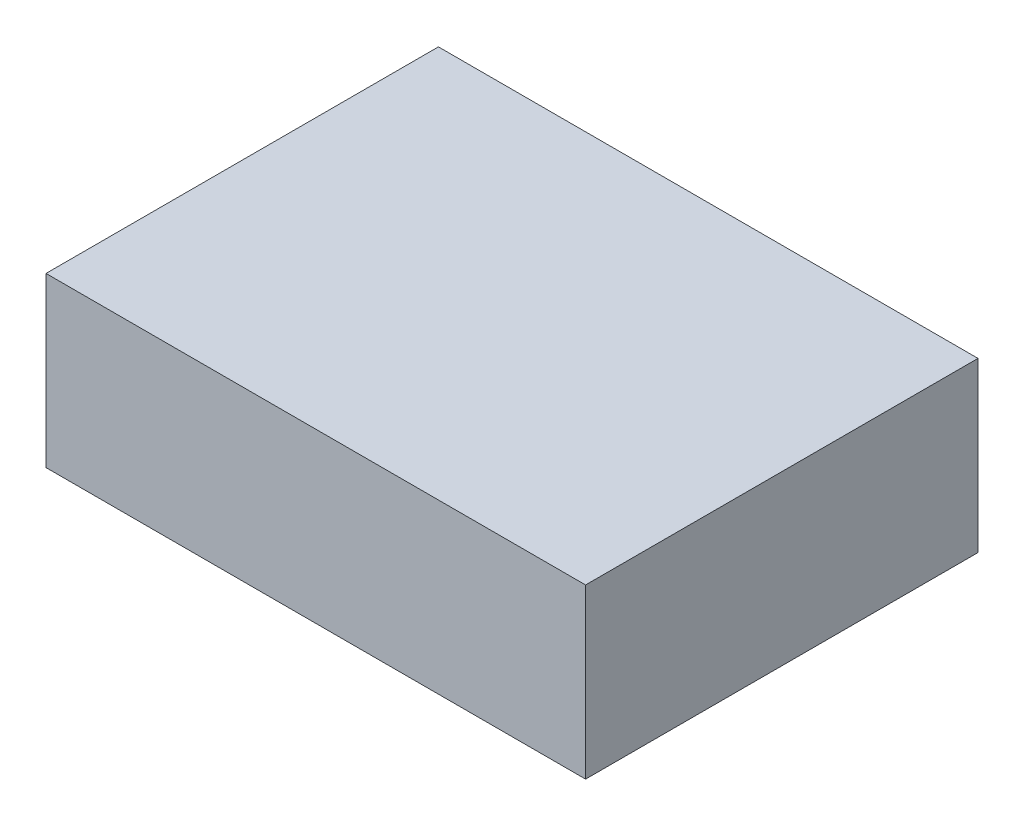
SolidWorks part; units mm, degrees
material "Pine"
ref_plane "Front Plane" through (0, 0, 0) normal (0, 0, 1) x (1, 0, 0)
ref_plane "Top Plane" through (0, 0, 0) normal (0, 1, 0) x (1, 0, 0)
ref_plane "Right Plane" through (0, 0, 0) normal (1, 0, 0) x (0, 0, -1)
sketch "Sketch1" plane through (0, 0, 0) normal (0, 1, 0) x (1, 0, 0)
  line L1 (0, 0) -> (122.2375, 0)
  line L2 (0, 0) -> (0, 88.9)
  line L3 (0, 88.9) -> (122.2375, 88.9)
  line L4 (122.2375, 0) -> (122.2375, 88.9)
  dimension "D1" = 88.9
  dimension "D2" = 122.2375
extrude "Boss-Extrude1" add sketch "Sketch1" along normal blind 38.1
